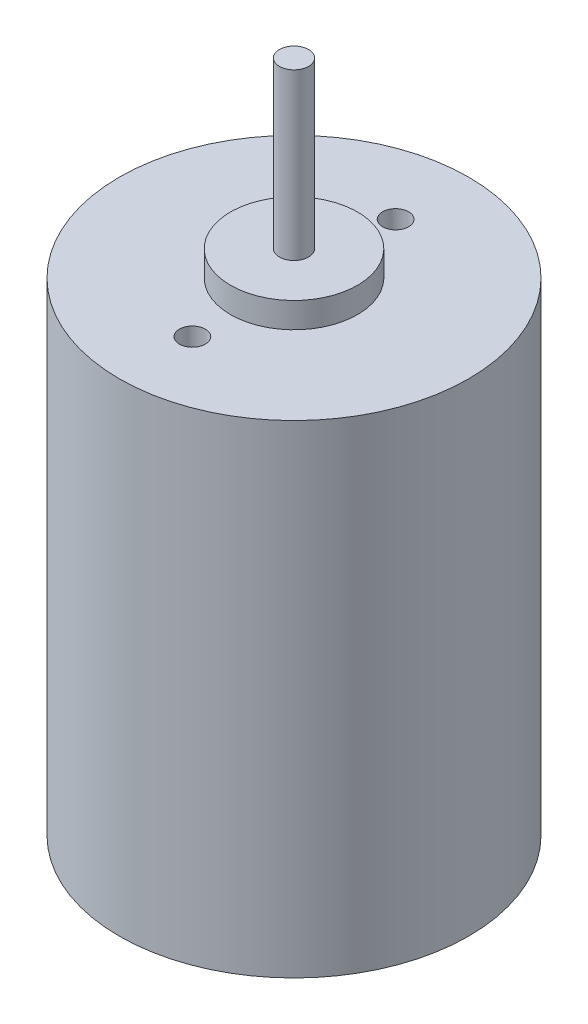
SolidWorks part; units mm, degrees
ref_plane "前视基准面" through (0, 0, 0) normal (0, 0, 1) x (1, 0, 0)
ref_plane "上视基准面" through (0, 0, 0) normal (0, 1, 0) x (1, 0, 0)
ref_plane "右视基准面" through (0, 0, 0) normal (1, 0, 0) x (0, 0, -1)
sketch "草图1" plane through (0, 0, 0) normal (0, 1, 0) x (1, 0, 0)
  circle A0 centre (0, 0) radius 13.75
  dimension "D1" = 27.5
extrude "凸台-拉伸1" add sketch "草图1" along normal blind 38
sketch "草图2" plane through (0, 38, 0) normal (0, 1, 0) x (1, 0, 0)
  circle A0 centre (0, 0) radius 5
  dimension "D1" = 10
extrude "凸台-拉伸2" add sketch "草图2" along normal blind 2
sketch "草图3" plane through (0, 40, 0) normal (0, 1, 0) x (1, 0, 0)
  circle A0 centre (0, 0) radius 1.15
  dimension "D1" = 2.3
extrude "凸台-拉伸3" add sketch "草图3" along normal blind 13
sketch "草图4" plane through (0, 38, 0) normal (0, 1, 0) x (1, 0, 0)
  line L0 (0, 8) -> (0, 0) construction
  line L1 (0, 0) -> (0, -8) construction
  dimension "D1" = 8
  dimension "D2" = 8
hole_wizard "M2.5 螺纹孔1" positions "草图5" profile "草图6" tap size "M2.5" standard "GB"
sketch "草图5" plane through (0, 38, 0) normal (0, 1, 0) x (1, 0, 0)
  point P0 (0, 8)
  point P3 (0, -8)
cosmetic thread "孔螺蚊线1" parameters "D1"=2.4, "D2"=2.5
cosmetic thread "孔螺蚊线2" parameters "D1"=2.4, "D2"=2.5
sketch "草图6" plane through (0, 38, -8) normal (1, 0, 0) x (0, 0, 1)
  line L0 (0, 0) -> (0, 4.3659)
  line L1 (0, 4.3659) -> (1.025, 3.75)
  line L2 (1.025, 3.75) -> (1.025, 0)
  line L5 (1.025, 0) -> (0, 0)
  line L10 (0, 4.3659) -> (-1.025, 3.75) construction
  line L11 (0, -6.35) -> (0, 107.95) construction
  dimension "螺纹孔钻头直径" = 2.05
  dimension "螺纹孔钻头深度" = 3.75
  dimension "导头角度" = 118
